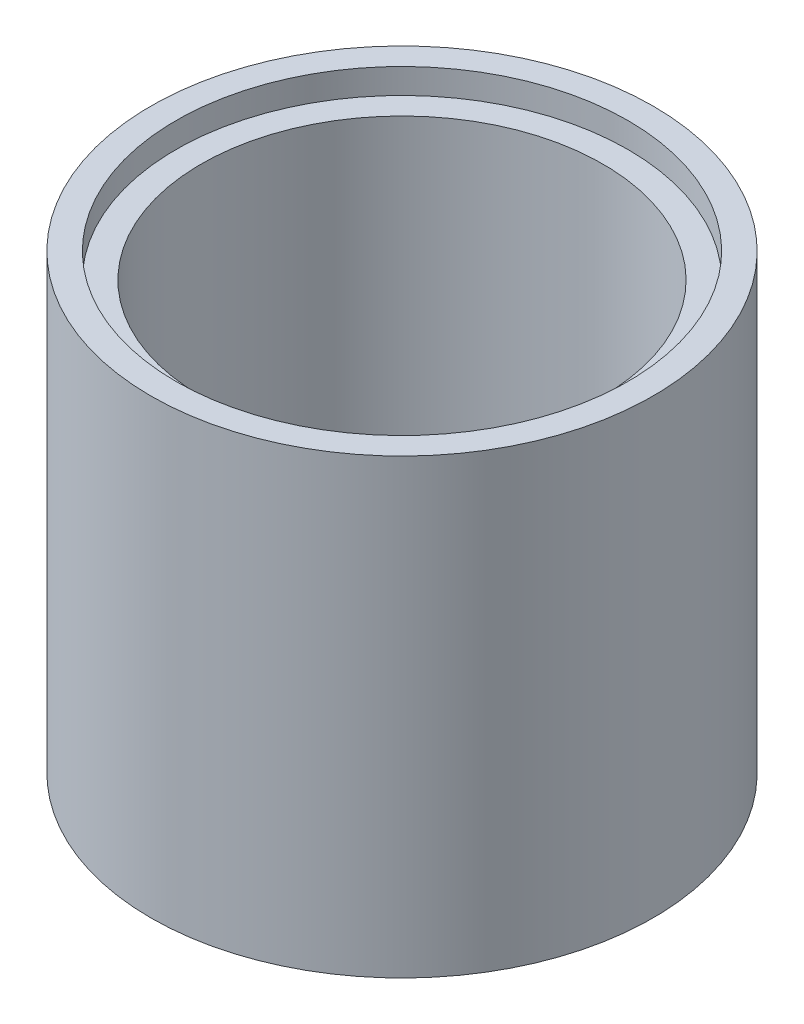
SolidWorks part; units mm, degrees
ref_plane "Alzado" through (0, 0, 0) normal (0, 0, 1) x (1, 0, 0)
ref_plane "Planta" through (0, 0, 0) normal (0, 1, 0) x (1, 0, 0)
ref_plane "Vista lateral" through (0, 0, 0) normal (1, 0, 0) x (0, 0, -1)
sketch "Croquis1" plane through (0, 0, 0) normal (0, 1, 0) x (1, 0, 0)
  circle A0 centre (0, 0) radius 25
  dimension "D1" = 50
extrude "Saliente-Extruir1" add sketch "Croquis1" along normal blind 45
sketch "Croquis2" plane through (0, 45, 0) normal (0, 1, 0) x (1, 0, 0)
  circle A0 centre (0, 0) radius 20
  dimension "D1" = 40
extrude "Cortar-Extruir1" cut sketch "Croquis2" against normal blind 40
sketch "Croquis3" plane through (0, 45, 0) normal (0, 1, 0) x (1, 0, 0)
  circle A0 centre (0, 0) radius 22.5
  dimension "D1" = 45
extrude "Cortar-Extruir2" cut sketch "Croquis3" against normal blind 2.5
